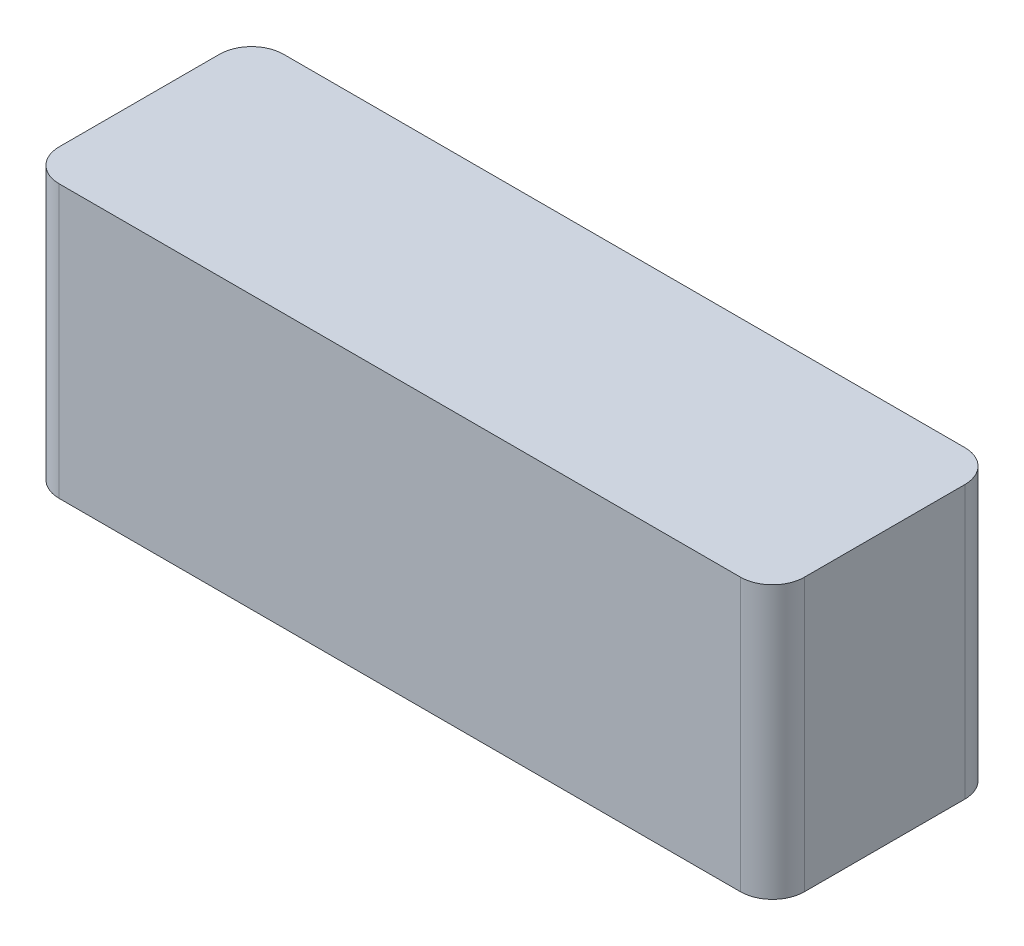
SolidWorks part; units mm, degrees
ref_plane "前视基准面" through (0, 0, 0) normal (0, 0, 1) x (1, 0, 0)
ref_plane "上视基准面" through (0, 0, 0) normal (0, 1, 0) x (1, 0, 0)
ref_plane "右视基准面" through (0, 0, 0) normal (1, 0, 0) x (0, 0, -1)
sketch "草图1" plane through (0, 0, 0) normal (0, 0, 1) x (1, 0, 0)
  line L0 (-93, 0) -> (93, 0) construction
  line L1 (-93, 34) -> (93, 34)
  line L2 (-93, 34) -> (-93, -34)
  line L3 (-93, -34) -> (93, -34)
  line L4 (93, 34) -> (93, -34)
  dimension "D1" = 186
  dimension "D2" = 68
extrude "凸台-拉伸1" add sketch "草图1" along normal blind 56
fillet "圆角1" radius 8 4 edges at (-93, 0, 0) (-93, 0, 56) (93, 0, 0) (93, 0, 56)
